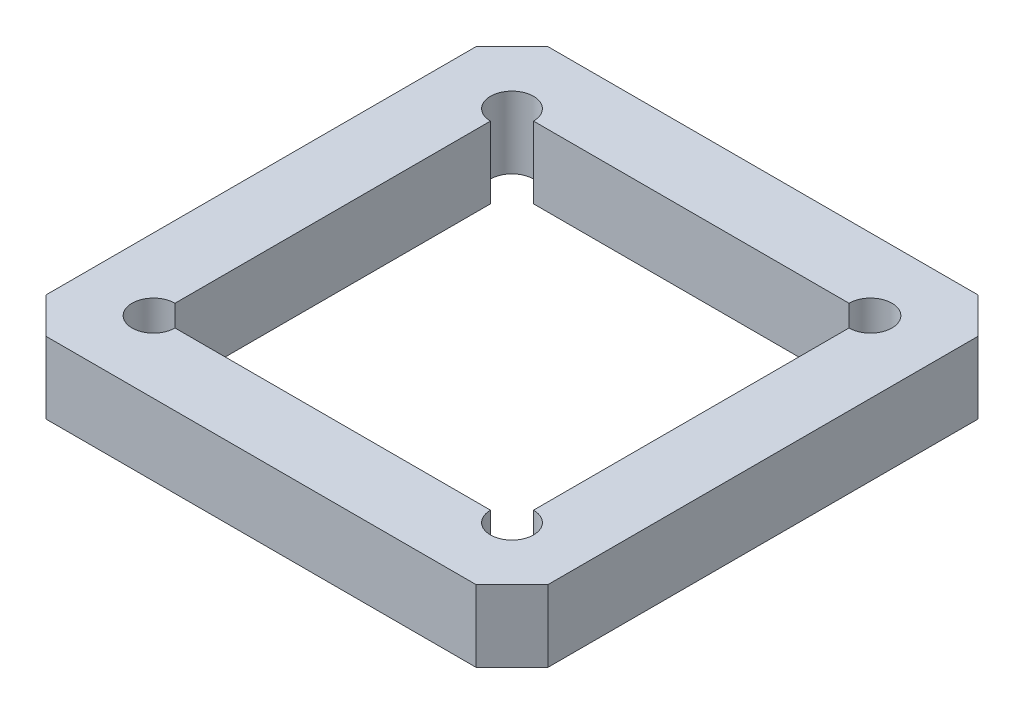
SolidWorks part; units mm, degrees
ref_plane "Front Plane" through (0, 0, 0) normal (0, 0, 1) x (1, 0, 0)
ref_plane "Top Plane" through (0, 0, 0) normal (0, 1, 0) x (1, 0, 0)
ref_plane "Right Plane" through (0, 0, 0) normal (1, 0, 0) x (0, 0, -1)
sketch "Sketch1" plane through (0, 0, 0) normal (0, 1, 0) x (1, 0, 0)
  line L0 (2.7816, 5) -> (7.7816, 0)
  line L1 (7.7816, 0) -> (67.7816, 0)
  line L2 (67.7816, 0) -> (72.7816, 5)
  line L3 (72.7816, 5) -> (72.7816, 65)
  line L4 (72.7816, 65) -> (67.7816, 70)
  line L5 (67.7816, 70) -> (7.7816, 70)
  line L6 (7.7816, 70) -> (2.7816, 65)
  line L7 (2.7816, 65) -> (2.7816, 5)
  line L17 (12.7816, 60) -> (62.7816, 60)
  line L18 (12.7816, 60) -> (12.7816, 10)
  line L19 (12.7816, 10) -> (62.7816, 10)
  line L20 (62.7816, 60) -> (62.7816, 10)
  circle A0 centre (12.7816, 10) radius 3
  circle A1 centre (62.7816, 10) radius 3
  circle A2 centre (62.7816, 60) radius 3
  circle A3 centre (12.7816, 60) radius 3
  point P2 (37.7816, 70)
  point P10 (37.7816, 0)
  point P11 (2.7816, 35)
  point P12 (72.7816, 35)
  dimension "D10" = 6
  dimension "D1" = 60
  dimension "D2" = 70
  dimension "D3" = 5
  dimension "D4" = 60
  dimension "D5" = 5
  dimension "D6" = 10
  dimension "D7" = 10
  dimension "D8" = 10
  dimension "D9" = 10
extrude "Boss-Extrude1" add sketch "Sketch1" along normal blind 10 contours L6 L7 L0 L1 L2 L3 L4 L5 A3 L17 A2 L20 A1 L19 A0 L18
sketch "Sketch2" plane through (0, 0, 0) normal (0, -1, 0) x (1, 0, 0)
  line L6 (2.7816, -65) -> (2.7816, -5) construction
  line L7 (7.7816, 0) -> (67.7816, 0) construction
  line L8 (72.7816, -5) -> (72.7816, -65) construction
  line L9 (67.7816, -70) -> (7.7816, -70) construction
  circle A0 centre (22.7816, -5) radius 4
  circle A1 centre (52.6811, -5) radius 4
  circle A2 centre (67.7816, -20) radius 4
  circle A3 centre (67.7816, -50) radius 4
  circle A4 centre (52.6811, -64.8995) radius 4
  circle A5 centre (22.7816, -64.8995) radius 4
  circle A6 centre (7.8318, -50) radius 4
  circle A7 centre (7.8318, -20) radius 4
  point P18 (0, 0)
  point P21 (0, 0)
  point P22 (0, 0)
  point P23 (0, 0)
  point P24 (0, 0)
  point P27 (0, 0)
  point P28 (0, 0)
  point P29 (0, 0)
  point P30 (0, 0)
  point P31 (0, 0)
  dimension "D1" = 20
  dimension "D3" = 8
  dimension "D6" = 20
  dimension "D7" = 29.8995
  dimension "D2" = 5
  dimension "D4" = 5
  dimension "D5" = 20
extrude "Cut-Extrude1" cut sketch "Sketch2" against normal blind 5
